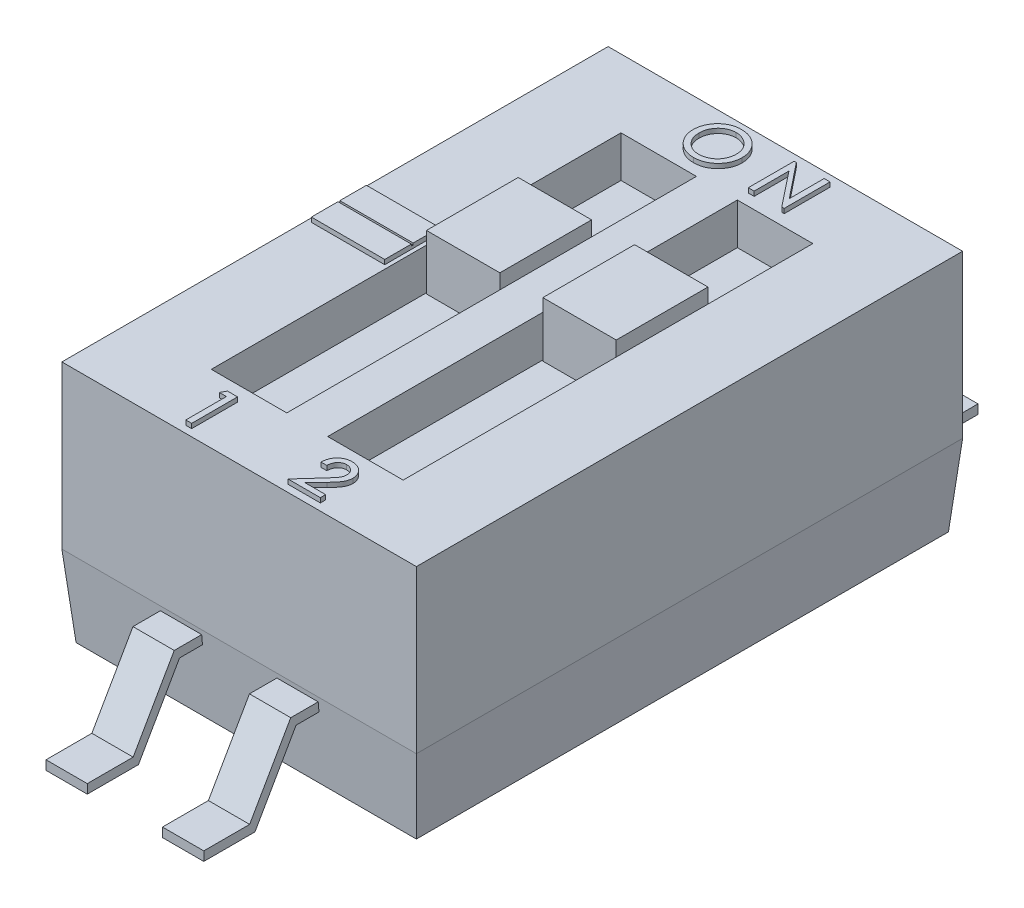
SolidWorks part; units mm, degrees
ref_plane "Front Plane" through (0, 0, 0) normal (0, 0, 1) x (1, 0, 0)
ref_plane "Top Plane" through (0, 0, 0) normal (0, 1, 0) x (1, 0, 0)
ref_plane "Right Plane" through (0, 0, 0) normal (1, 0, 0) x (0, 0, -1)
sketch "Sketch1" plane through (0, 0, 0) normal (0, 1, 0) x (1, 0, 0)
  line L1 (0, 0) -> (3.71, 0)
  line L2 (0, 0) -> (0, 5.8)
  line L3 (0, 5.8) -> (3.71, 5.8)
  line L4 (3.71, 0) -> (3.71, 5.8)
  dimension "D1" = 5.8
  dimension "D2" = 3.71
extrude "Boss-Extrude1" add sketch "Sketch1" along normal blind 0.8833 draft 5 draft outward yes
sketch "Sketch2" plane through (0, 0.8833, 0) normal (0, 1, 0) x (1, 0, 0)
  line L1 (-0.0773, 5.8773) -> (3.7873, 5.8773)
  line L2 (-0.0773, 5.8773) -> (-0.0773, -0.0773)
  line L3 (-0.0773, -0.0773) -> (3.7873, -0.0773)
  line L4 (3.7873, 5.8773) -> (3.7873, -0.0773)
extrude "Boss-Extrude2" add sketch "Sketch2" along normal blind 1.7667
sketch "Sketch3" plane through (3.7873, 2.0934, 0) normal (-1, 0, 0) x (0, 0, -1)
  line L0 (2.9, 1.2101) -> (7.12, 1.2101) construction
  line L1 (-0.0773, 1.2101) -> (5.8773, 1.2101) construction
  line L2 (2.9, 1.2101) -> (-1.32, 1.2101) construction
  line L6 (6.62, 2.0434) -> (7.12, 2.0434)
  line L7 (5.8607, 1.2601) -> (6.1721, 1.2601)
  line L8 (6.62, 2.0434) -> (6.1721, 1.2601)
extrude "Extrude-Thin1" add sketch "Sketch3" along normal mid plane 0.45 from offset 1.3 thin thin type one direction reverse wall 0.1
pattern_linear "LPattern1" count 2 spacing 1.27 along (-1, 0, 0) of "Extrude-Thin1"
ref_plane "Plane1" through (0, 0, -2.9) normal (0, 0, 1) x (1, 0, 0)
mirror "Mirror1" about plane through (0, 0, -2.9) normal (0, 0, 1) of "Extrude-Thin1", "LPattern1"
sketch "Sketch4" plane through (0, 2.65, 0) normal (0, 1, 0) x (1, 0, 0)
  line L1 (0.8073, 5.133) -> (1.63, 5.133)
  line L6 (0.8073, 0.667) -> (1.63, 0.667)
  line L7 (0.8073, 5.133) -> (0.8073, 0.667)
  line L11 (2.0759, 5.133) -> (2.8986, 5.133)
  line L12 (1.63, 5.133) -> (1.63, 0.667)
  line L13 (2.0759, 0.667) -> (2.8986, 0.667)
  line L14 (2.0759, 5.133) -> (2.0759, 0.667)
  line L15 (2.8986, 5.133) -> (2.8986, 0.667)
extrude "Cut-Extrude1" cut sketch "Sketch4" against normal blind 0.45
sketch "Sketch7" plane through (0, 2.2, 0) normal (0, 1, 0) x (1, 0, 0)
  line L5 (0.8186, 4.0012) -> (0.8186, 3.0012)
  line L6 (0.8186, 4.0012) -> (1.6186, 4.0012)
  line L7 (0.8186, 3.0012) -> (1.6186, 3.0012)
  line L9 (1.6186, 3.0012) -> (1.6186, 4.0012)
  line L11 (2.0873, 4.0012) -> (2.0873, 3.0012)
  line L12 (2.0873, 4.0012) -> (2.8873, 4.0012)
  line L13 (2.0873, 3.0012) -> (2.8873, 3.0012)
  line L14 (2.8873, 3.0012) -> (2.8873, 4.0012)
extrude "Boss-Extrude3" add sketch "Sketch7" along normal blind 0.6
sketch "Sketch9" plane through (0, 2.65, 0) normal (0, 1, 0) x (1, 0, 0)
  line L0 (0.8073, 0) -> (1.63, 0) construction
  line L1 (0.8073, 5.2588) -> (2.8986, 5.2588) construction
  line L2 (2.0759, 0) -> (2.8986, 0) construction
  line L7 (0.365, 3.2) -> (-0.035, 3.2)
  line L8 (-0.035, 3.2) -> (-0.035, 2.6)
  line L9 (-0.035, 2.6) -> (0.765, 2.6)
  line L10 (0.765, 2.6) -> (0.765, 3.2)
  line L11 (0.765, 3.2) -> (0.365, 3.2)
  text T0 "ON" font "Century Gothic" height 0.5
  text T1 "1" font "Century Gothic" height 0.5
  text T2 "2" font "Century Gothic" height 0.5
extrude "Boss-Extrude4" add sketch "Sketch9" along normal blind 0.05
sketch "Sketch10" plane through (0, 2.7, 0) normal (0, 1, 0) x (1, 0, 0)
  line L0 (-0.0365, 2.91) -> (0.7668, 2.91)
  line L3 (0.7668, 2.89) -> (-0.0365, 2.89)
  line L4 (-0.0365, 2.91) -> (-0.0365, 2.89)
  line L11 (0.7668, 2.91) -> (0.7668, 2.89)
extrude "Cut-Extrude2" cut sketch "Sketch10" against normal blind 0.02 contours L4 L3 L11 L0
